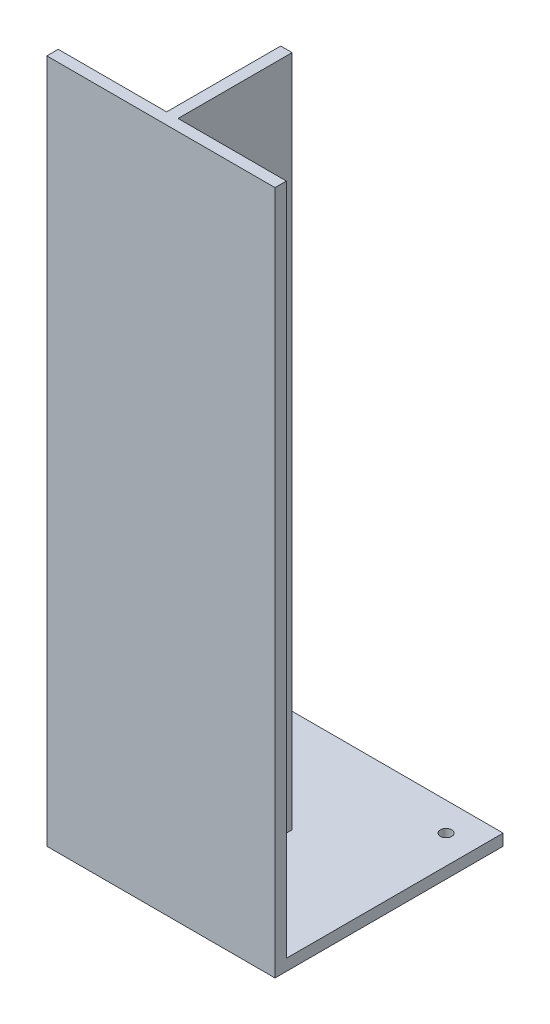
SolidWorks part; units mm, degrees
material "1023 Chapa de acero al carbono (SS)"
ref_plane "Alzado" through (0, 0, 0) normal (0, 0, 1) x (1, 0, 0)
ref_plane "Planta" through (0, 0, 0) normal (0, 1, 0) x (1, 0, 0)
ref_plane "Vista lateral" through (0, 0, 0) normal (1, 0, 0) x (0, 0, -1)
sketch "Croquis2" plane through (0, 0, 0) normal (1, 0, 0) x (0, 0, -1)
  line L0 (0, 293.3544) -> (0, -306.6456)
  line L1 (0, -306.6456) -> (200, -306.6456)
  line L2 (200, -306.6456) -> (200, -296.6456)
  line L3 (200, -296.6456) -> (10, -296.6456)
  line L4 (10, -296.6456) -> (10, 293.3544)
  line L5 (10, 293.3544) -> (0, 293.3544)
  dimension "D1" = 600
  dimension "D2" = 200
  dimension "D3" = 10
  dimension "D4" = 10
extrude "Saliente-Extruir1" add sketch "Croquis2" against normal blind 200
ref_plane "Plano2" through (0, -297, 0) normal (0, 1, 0) x (1, 0, 0)
sketch "Croquis5" plane through (0, -297, 0) normal (0, 1, 0) x (1, 0, 0)
  line L0 (-100, 10) -> (-100, 110) construction
  line L1 (-200, 10) -> (0, 10) construction
  line L2 (-100, 10) -> (-105, 10)
  line L3 (-105, 10) -> (-105, 110)
  line L4 (-105, 110) -> (-95, 110)
  line L5 (-95, 110) -> (-95, 10)
  line L6 (-200, 10) -> (0, 10) construction
  line L7 (-95, 10) -> (-100, 10)
  dimension "D1" = 100
  dimension "D2" = 5
  dimension "D3" = 5
extrude "Saliente-Extruir2" add sketch "Croquis5" along normal through all
sketch "Croquis6" plane through (0, -297, 0) normal (0, 1, 0) x (1, 0, 0)
  circle A0 centre (-175, 175) radius 5
  circle A1 centre (-25, 175) radius 5
  circle A2 centre (-25, 25) radius 5
  circle A3 centre (-175, 25) radius 5
  point P8 (-100, 100)
  dimension "D2" = 10
  dimension "D3" = 10
  dimension "D4" = 10
  dimension "D5" = 10
  dimension "D1" = 150
extrude "Cortar-Extruir1" cut sketch "Croquis6" along normal through all both and the other way through all
